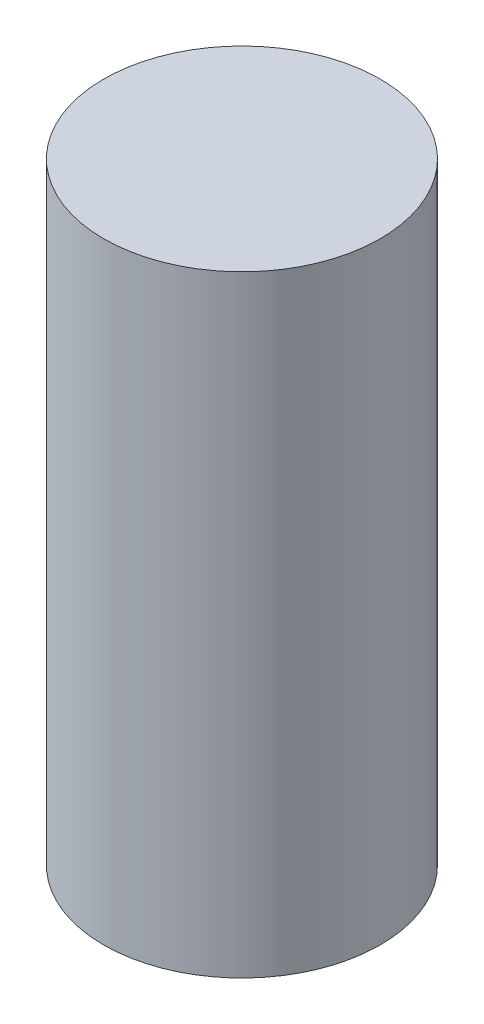
SolidWorks part; units mm, degrees
ref_plane "Front Plane" through (0, 0, 0) normal (0, 0, 1) x (1, 0, 0)
ref_plane "Top Plane" through (0, 0, 0) normal (0, 1, 0) x (1, 0, 0)
ref_plane "Right Plane" through (0, 0, 0) normal (1, 0, 0) x (0, 0, -1)
sketch "Sketch1" plane through (0, 0, 0) normal (0, 1, 0) x (1, 0, 0)
  circle A0 centre (0, 0) radius 2.6
  dimension "D1" = 5.2
extrude "Boss-Extrude1" add sketch "Sketch1" along normal blind 11.5
